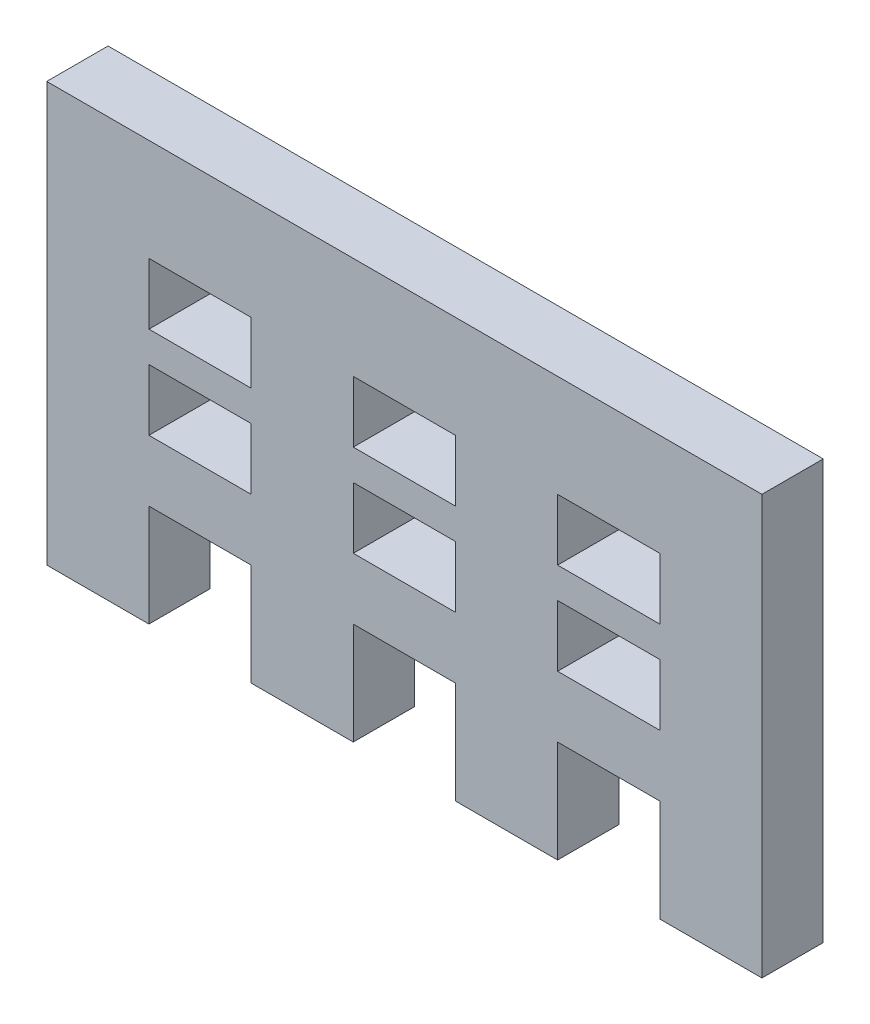
SolidWorks part; units mm, degrees
ref_plane "Plan de face" through (0, 0, 0) normal (0, 0, 1) x (1, 0, 0)
ref_plane "Plan de dessus" through (0, 0, 0) normal (0, 1, 0) x (1, 0, 0)
ref_plane "Plan de droite" through (0, 0, 0) normal (1, 0, 0) x (0, 0, -1)
sketch "Esquisse1" plane through (0, 0, 0) normal (0, 0, 1) x (1, 0, 0)
  line L0 (-25, 0) -> (-25, -5)
  line L1 (-35, 3) -> (0, 3)
  line L2 (-35, 3) -> (-35, 0)
  line L3 (-35, 0) -> (0, 0)
  line L4 (0, 3) -> (0, 0)
  line L5 (-35, 0) -> (-30, 0)
  line L6 (-35, 0) -> (-35, -5)
  line L7 (-35, -5) -> (-30, -5)
  line L8 (-30, 0) -> (-30, -5)
  line L9 (-25, -5) -> (-20, -5)
  line L10 (-20, 0) -> (-20, -5)
  line L11 (-15, 0) -> (-15, -5)
  line L12 (-15, -5) -> (-10, -5)
  line L13 (-10, 0) -> (-10, -5)
  line L14 (-5, 0) -> (-5, -5)
  line L15 (-5, -5) -> (0, -5)
  line L16 (0, 0) -> (0, -5)
  line L17 (-25, 6) -> (-20, 6)
  line L18 (-35, 3) -> (-30, 3)
  line L19 (-35, 3) -> (-35, 6)
  line L20 (-35, 6) -> (-30, 6)
  line L21 (-30, 3) -> (-30, 6)
  line L22 (-25, 3) -> (-25, 6)
  line L23 (-20, 3) -> (-20, 6)
  line L24 (-15, 6) -> (-10, 6)
  line L25 (-15, 3) -> (-15, 6)
  line L26 (-10, 3) -> (-10, 6)
  line L27 (-5, 6) -> (0, 6)
  line L28 (-5, 3) -> (-5, 6)
  line L29 (0, 3) -> (0, 6)
  line L30 (-25, 7.5) -> (-25, 10.5)
  line L31 (-35, 6) -> (0, 6)
  line L32 (-35, 6) -> (-35, 7.5)
  line L33 (-35, 7.5) -> (0, 7.5)
  line L34 (0, 6) -> (0, 7.5)
  line L35 (-35, 7.5) -> (-30, 7.5)
  line L36 (-35, 7.5) -> (-35, 10.5)
  line L37 (-35, 10.5) -> (-30, 10.5)
  line L38 (-30, 7.5) -> (-30, 10.5)
  line L39 (-25, 10.5) -> (-20, 10.5)
  line L40 (-20, 7.5) -> (-20, 10.5)
  line L41 (-15, 7.5) -> (-15, 10.5)
  line L42 (-15, 10.5) -> (-10, 10.5)
  line L43 (-10, 7.5) -> (-10, 10.5)
  line L44 (-5, 7.5) -> (-5, 10.5)
  line L45 (-5, 10.5) -> (0, 10.5)
  line L46 (0, 7.5) -> (0, 10.5)
  line L48 (-35, 10.5) -> (0, 10.5)
  line L49 (-35, 10.5) -> (-35, 15.5)
  line L50 (-35, 15.5) -> (0, 15.5)
  line L51 (0, 10.5) -> (0, 15.5)
  dimension "D1" = 35
  dimension "D2" = 3
  dimension "D3" = 5
  dimension "D4" = 5
  dimension "D6" = 5
  dimension "D7" = 3
  dimension "D8" = 4
  dimension "D9" = 1.5
  dimension "D10" = 3
  dimension "D11" = 5
  dimension "D12" = 4
  dimension "D13" = 5
  dimension "D5" = 4
extrude "Boss.-Extru.1" add sketch "Esquisse1" along normal blind 3 contours L8 L3 L6 L7 | L10 L3 L0 L9 | L13 L3 L11 L12 | L16 L3 L14 L15 | L4 L1 L2 L3 | L1 L29 L27 L28 | L1 L26 L24 L25 | L1 L23 L17 L22 | L1 L21 L20 L19 | L27 L34 L33 L32 L20 L31 L17 L24 | L33 L38 L37 L36 | L33 L40 L39 L30 | L33 L43 L42 L41 | L33 L46 L45 L44 | L45 L51 L50 L49 L37 L48 L39 L42
